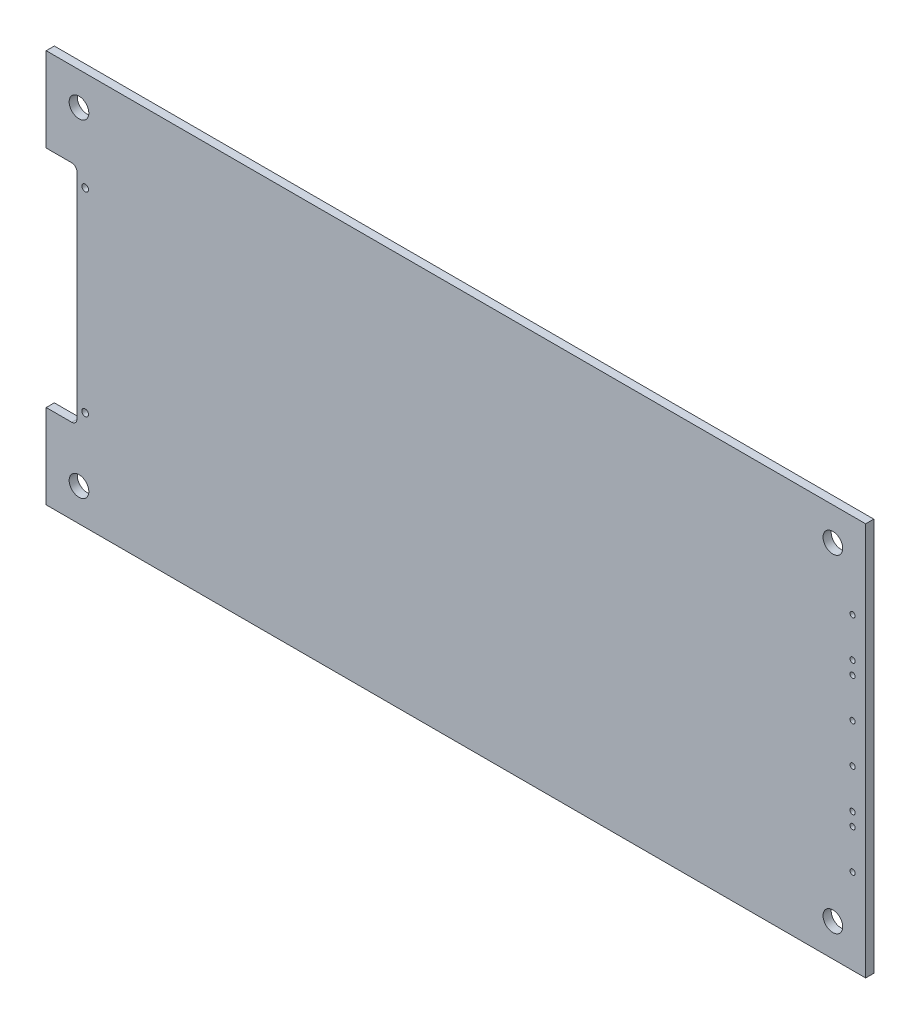
SolidWorks part; units mm, degrees
ref_plane "Front" through (0, 0, 0) normal (0, 0, 1) x (1, 0, 0)
ref_plane "Top" through (0, 0, 0) normal (0, 1, 0) x (1, 0, 0)
ref_plane "Right" through (0, 0, 0) normal (1, 0, 0) x (0, 0, -1)
sketch "Sketch1" plane through (0, 0, 0) normal (0, 0, 1) x (1, 0, 0)
  line L1 (0, 0) -> (158.75, 0)
  line L2 (0, 0) -> (0, -76.2)
  line L3 (0, -76.2) -> (158.75, -76.2)
  line L4 (158.75, 0) -> (158.75, -76.2)
  dimension "D1" = 158.75
  dimension "D2" = 76.2
extrude "Extrude1" add sketch "Sketch1" along normal blind 1.5748
sketch "Sketch2" plane through (0, 0, 1.5748) normal (0, 0, 1) x (1, 0, 0)
  line L0 (158.75, -76.2) -> (158.75, 0) construction
  line L1 (158.75, 0) -> (0, 0) construction
  line L2 (0, 0) -> (0, -76.2) construction
  line L3 (0, -76.2) -> (158.75, -76.2) construction
  circle A0 centre (152.4, -6.35) radius 1.905
  circle A1 centre (6.35, -6.35) radius 1.905
  circle A2 centre (152.4, -69.85) radius 1.905
  circle A3 centre (6.35, -69.85) radius 1.905
  dimension "D1" = 6.35
  dimension "D5" = 3.81
  dimension "D6" = 3.81
  dimension "D11" = 3.81
  dimension "D12" = 3.81
  dimension "D2" = 6.35
  dimension "D3" = 6.35
  dimension "D4" = 6.35
  dimension "D7" = 6.35
  dimension "D8" = 6.35
  dimension "D9" = 6.35
  dimension "D10" = 6.35
extrude "Cut-Extrude2" cut sketch "Sketch2" against normal blind 1.5748
sketch "Sketch4" plane through (0, 0, 1.5748) normal (0, 0, 1) x (1, 0, 0)
  line L0 (0, -76.2) -> (158.75, -76.2) construction
  line L1 (0, 0) -> (0, -76.2) construction
  line L2 (158.75, 0) -> (0, 0) construction
  line L3 (0, -16.335) -> (4.95, -16.335)
  line L4 (5.95, -58.865) -> (5.95, -17.335)
  line L5 (0, -16.335) -> (0, -59.865)
  line L6 (0, -59.865) -> (4.95, -59.865)
  circle A0 centre (7.55, -19.2349) radius 0.65
  circle A1 centre (7.55, -56.9651) radius 0.65
  arc A2 (4.95, -16.335) -> (5.95, -17.335) centre (4.95, -17.335) cw
  arc A3 (5.95, -58.865) -> (4.95, -59.865) centre (4.95, -58.865) cw
  dimension "D1" = 1.3
  dimension "D2" = 1.3
  dimension "D10" = 1
  dimension "D11" = 1
  dimension "D3" = 19.2349
  dimension "D4" = 7.55
  dimension "D5" = 19.2349
  dimension "D6" = 7.55
  dimension "D7" = 37.7302
  dimension "D8" = 43.53
  dimension "D9" = 5.95
  dimension "D12" = 16.335
  dimension "D13" = 16.335
extrude "Cut-Extrude3" cut sketch "Sketch4" against normal blind 1.5748
sketch "Sketch5" plane through (0, 0, 1.5748) normal (0, 0, 1) x (1, 0, 0)
  line L0 (0, -76.2) -> (158.75, -76.2) construction
  line L1 (158.75, -76.2) -> (158.75, 0) construction
  circle A0 centre (156.21, -59.69) radius 0.508
  circle A1 centre (156.21, -52.07) radius 0.508
  circle A2 centre (156.21, -49.53) radius 0.508
  circle A3 centre (156.21, -41.91) radius 0.508
  dimension "D1" = 1.016
  dimension "D7" = 1.016
  dimension "D8" = 1.016
  dimension "D9" = 1.016
  dimension "D2" = 16.51
  dimension "D3" = 2.54
  dimension "D4" = 7.62
  dimension "D5" = 2.54
  dimension "D6" = 7.62
extrude "transceiver holes" cut sketch "Sketch5" against normal blind 2.54
pattern_linear "LPattern1" count 2 spacing 25.4 along (0, 1, 0) of "transceiver holes"
